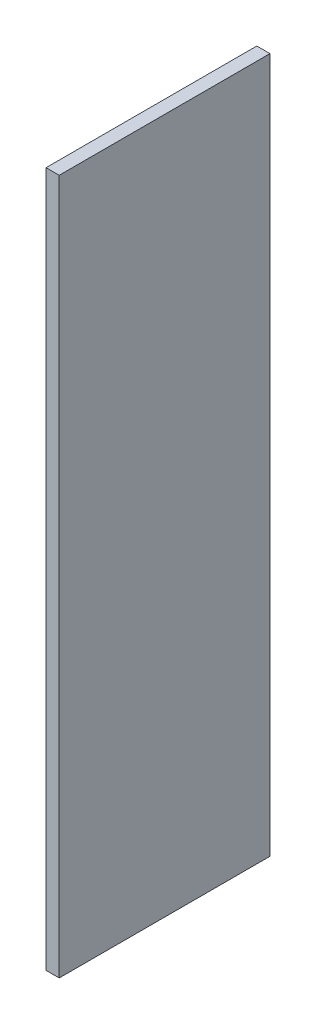
SolidWorks part; units mm, degrees
ref_plane "Front Plane" through (0, 0, 0) normal (0, 0, 1) x (1, 0, 0)
ref_plane "Top Plane" through (0, 0, 0) normal (0, 1, 0) x (1, 0, 0)
ref_plane "Right Plane" through (0, 0, 0) normal (1, 0, 0) x (0, 0, -1)
sketch "Sketch1" plane through (0, 0, 0) normal (1, 0, 0) x (0, 0, -1)
  line L1 (20.3921, -892.2196) -> (-267.6079, -892.2196)
  line L2 (20.3921, -892.2196) -> (20.3921, 57.7804)
  line L3 (20.3921, 57.7804) -> (-267.6079, 57.7804)
  line L4 (-267.6079, -892.2196) -> (-267.6079, 57.7804)
  line L5 (20.3921, -892.2196) -> (-267.6079, 57.7804) construction
  line L6 (20.3921, 57.7804) -> (-267.6079, -892.2196) construction
  point P0 (-123.6079, -417.2196)
  dimension "D1" = 288
  dimension "D2" = 950
extrude "Boss-Extrude1" add sketch "Sketch1" along normal blind 18
equation "\"H_POLKI\"=950"
equation "\"D2@Sketch1\"=\"H_POLKI\""
equation "\"DSP_WIDTH\"=18"
equation "\"D1@Boss-Extrude1\"=\"DSP_WIDTH\""
